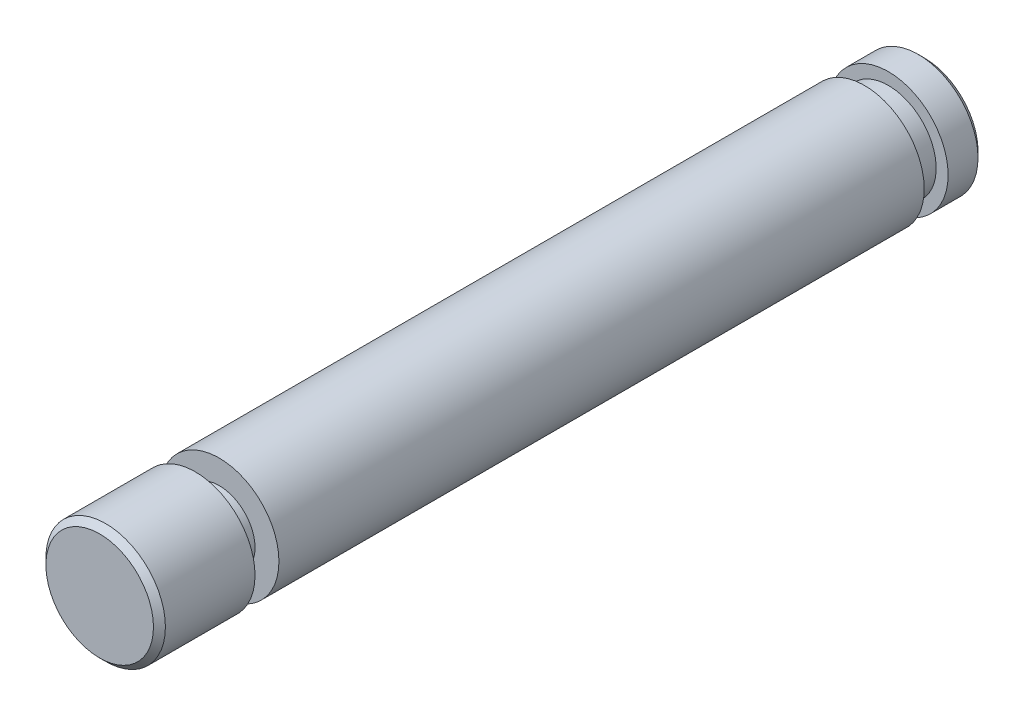
SolidWorks part; units mm, degrees
ref_plane "Front Plane" through (0, 0, 0) normal (0, 0, 1) x (1, 0, 0)
ref_plane "Top Plane" through (0, 0, 0) normal (0, 1, 0) x (1, 0, 0)
ref_plane "Right Plane" through (0, 0, 0) normal (1, 0, 0) x (0, 0, -1)
sketch "Sketch1" plane through (0, 0, 0) normal (0, 0, 1) x (1, 0, 0)
  circle A0 centre (0, 0) radius 5
  point P3 (0, 0)
  dimension "D1" = 10
extrude "Boss-Extrude1" add sketch "Sketch1" along normal mid plane 69
sketch "Sketch2" plane through (0, 0, 34.5) normal (0, 0, 1) x (1, 0, 0)
  circle A0 centre (0, 0) radius 3
  circle A1 centre (0, 0) radius 5
  circle A2 centre (0, 0) radius 5
  dimension "D2" = 6
  dimension "D1" = 0
extrude "Cut-Extrude1" cut sketch "Sketch2" along normal blind 2 from offset 10 offset against normal yes
sketch "Sketch4" plane through (0, 0, -34.5) normal (0, 0, -1) x (-1, 0, 0)
  circle A0 centre (0, 0) radius 4
  circle A1 centre (0, 0) radius 5
  circle A2 centre (0, 0) radius 5
  dimension "D2" = 8
  dimension "D1" = 0
extrude "Cut-Extrude2" cut sketch "Sketch4" along normal blind 2 from offset 5 offset against normal yes
chamfer "Chamfer1" distance 0.5 angle 45 2 edges at (5, 0, -34.5) (5, 0, 34.5)
cosmetic thread "Cosmetic Thread1" parameters "D1"=7, "D2"=6.619
sketch "Sketch7" plane through (0, 0, 0) normal (1, 0, 0) x (0, 0, -1)
  line L0 (8, 0) -> (34.5, 0) construction
  line L1 (8, 1.5) -> (34.5, 1.5)
  line L2 (8, -1.5) -> (34.5, -1.5)
  line L3 (34.5, -4.5) -> (34.5, 4.5) construction
  line L4 (34.5, 1.5) -> (34.5, -1.5)
  arc A0 (8, 1.5) -> (8, -1.5) centre (8, 0) ccw
  point P3 (21.25, 0)
  dimension "D2" = 1.5
  dimension "D1" = 26.5
  dimension "D3" = 3
  dimension "D4" = 1.5
  dimension "D5" = 26.5
extrude "Cut-Extrude4" cut sketch "Sketch7" against normal through all from offset 3.2 contours L2 L4 L1 A0
